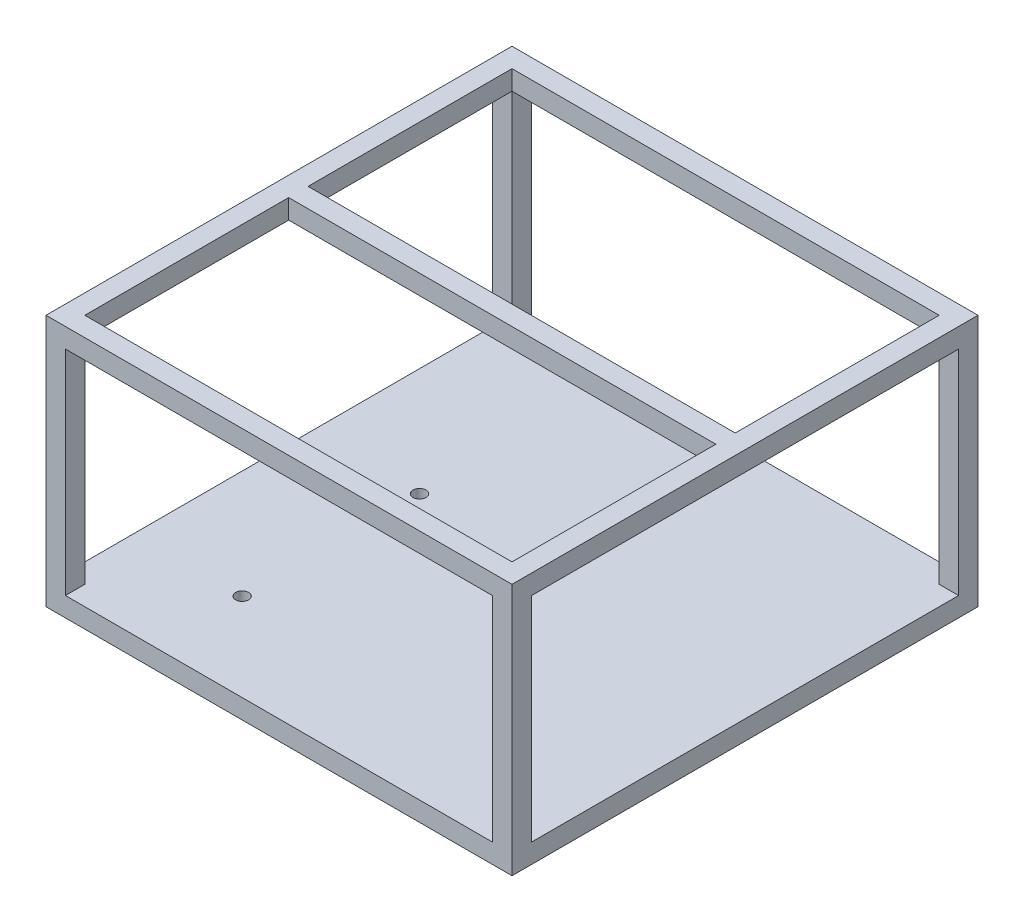
SolidWorks part; units mm, degrees
ref_plane "Front Plane" through (0, 0, 0) normal (0, 0, 1) x (1, 0, 0)
ref_plane "Top Plane" through (0, 0, 0) normal (0, 1, 0) x (1, 0, 0)
ref_plane "Right Plane" through (0, 0, 0) normal (1, 0, 0) x (0, 0, -1)
sketch "Sketch1" plane through (0, 0, 0) normal (0, 1, 0) x (1, 0, 0)
  line L1 (-35.4234, 121.5621) -> (116.9766, 121.5621)
  line L2 (-35.4234, 121.5621) -> (-35.4234, -30.8379)
  line L3 (-35.4234, -30.8379) -> (116.9766, -30.8379)
  line L4 (116.9766, 121.5621) -> (116.9766, -30.8379)
extrude "Boss-Extrude1" add sketch "Sketch1" along normal blind 6.35
sketch "Sketch2" plane through (0, 6.35, 0) normal (0, 1, 0) x (1, 0, 0)
  circle A0 centre (0, -2.125) radius 2.125
  circle A1 centre (0, 55.889) radius 2.125
extrude "Cut-Extrude1" cut sketch "Sketch2" against normal blind 6.35
sketch "Sketch3" plane through (0, 6.35, 0) normal (0, 1, 0) x (1, 0, 0)
  line L1 (116.9766, -30.8379) -> (110.6266, -30.8379)
  line L2 (116.9766, -30.8379) -> (116.9766, -24.4879)
  line L3 (116.9766, -24.4879) -> (110.6266, -24.4879)
  line L4 (110.6266, -30.8379) -> (110.6266, -24.4879)
  line L5 (-35.4234, -30.8379) -> (-29.0734, -30.8379)
  line L6 (-35.4234, -30.8379) -> (-35.4234, -24.4879)
  line L7 (-35.4234, -24.4879) -> (-29.0734, -24.4879)
  line L8 (-29.0734, -30.8379) -> (-29.0734, -24.4879)
  line L9 (-35.4234, 121.5621) -> (-29.0734, 121.5621)
  line L10 (-35.4234, 121.5621) -> (-35.4234, 115.2121)
  line L11 (-35.4234, 115.2121) -> (-29.0734, 115.2121)
  line L12 (-29.0734, 121.5621) -> (-29.0734, 115.2121)
  line L13 (116.9766, 121.5621) -> (110.6266, 121.5621)
  line L14 (116.9766, 121.5621) -> (116.9766, 115.2121)
  line L15 (116.9766, 115.2121) -> (110.6266, 115.2121)
  line L16 (110.6266, 121.5621) -> (110.6266, 115.2121)
  point P5 (110.6266, -27.6629)
  dimension "D1" = 6.35
  dimension "D2" = 6.35
  dimension "D3" = 6.35
  dimension "D4" = 6.35
  dimension "D5" = 6.35
  dimension "D6" = 6.35
  dimension "D7" = 6.35
  dimension "D8" = 6.35
extrude "Boss-Extrude2" add sketch "Sketch3" along normal blind 76.2
sketch "Sketch4" plane through (0, 0, 24.4879) normal (0, 0, -1) x (-1, 0, 0)
  line L0 (-116.9766, 82.55) -> (-116.9766, 6.35) construction
  line L1 (-110.6266, 82.55) -> (-116.9766, 82.55)
  line L2 (-110.6266, 82.55) -> (-110.6266, 76.1659)
  line L3 (-110.6266, 76.1659) -> (-116.9766, 76.1659)
  line L4 (-116.9766, 82.55) -> (-116.9766, 76.1659)
  line L5 (35.4234, 82.55) -> (35.4234, 6.35) construction
  line L6 (29.0734, 82.55) -> (35.4234, 82.55)
  line L7 (29.0734, 82.55) -> (29.0734, 76.1659)
  line L8 (29.0734, 76.1659) -> (35.4234, 76.1659)
  line L9 (35.4234, 82.55) -> (35.4234, 76.1659)
extrude "Boss-Extrude3" add sketch "Sketch4" along normal blind 139.7
sketch "Sketch5" plane through (-29.0734, 0, 0) normal (1, 0, 0) x (0, 0, -1)
  line L1 (-30.8379, 82.55) -> (-24.4879, 82.55)
  line L2 (-30.8379, 82.55) -> (-30.8379, 76.1659)
  line L3 (-30.8379, 76.1659) -> (-24.4879, 76.1659)
  line L4 (-24.4879, 82.55) -> (-24.4879, 76.1659)
  line L5 (121.5621, 82.55) -> (115.2121, 82.55)
  line L6 (121.5621, 82.55) -> (121.5621, 76.1659)
  line L7 (121.5621, 76.1659) -> (115.2121, 76.1659)
  line L8 (115.2121, 82.55) -> (115.2121, 76.1659)
extrude "Boss-Extrude4" add sketch "Sketch5" along normal blind 139.7
sketch "Sketch6" plane through (-29.0734, 0, 0) normal (1, 0, 0) x (0, 0, -1)
  line L1 (-24.4879, 82.55) -> (115.2121, 82.55) construction
  line L2 (115.2121, 76.1659) -> (-24.4879, 76.1659) construction
  line L4 (42.1721, 82.55) -> (48.5221, 82.55)
  line L5 (42.1721, 82.55) -> (42.1721, 76.1659)
  line L6 (42.1721, 76.1659) -> (48.5221, 76.1659)
  line L7 (48.5221, 82.55) -> (48.5221, 76.1659)
  dimension "D1" = 6.35
extrude "Boss-Extrude5" add sketch "Sketch6" along normal blind 139.7
